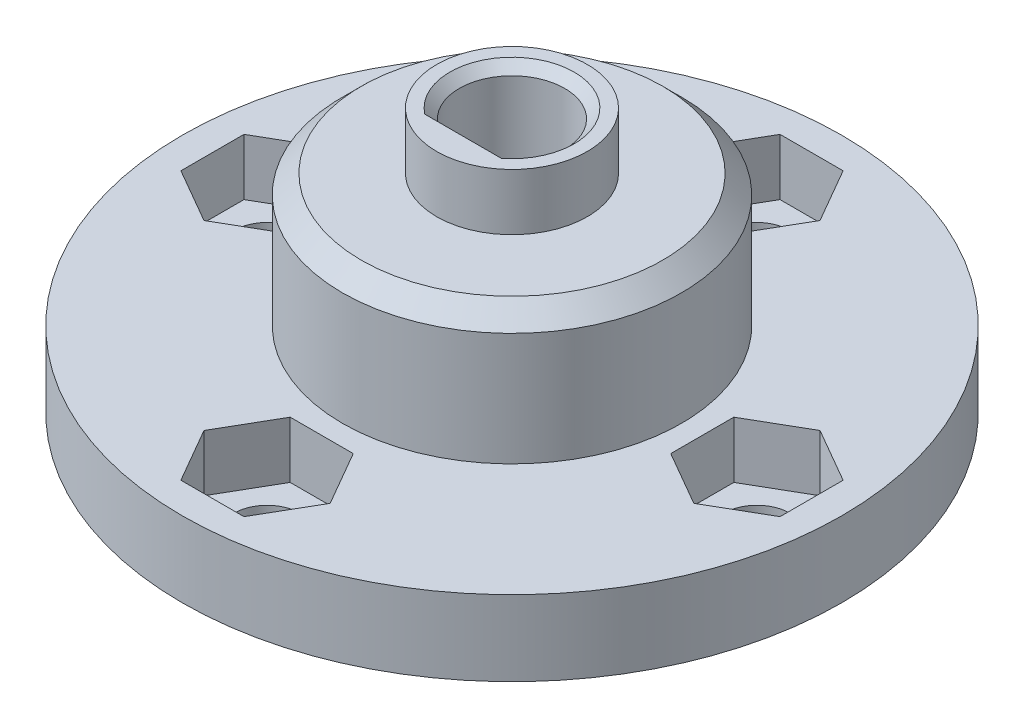
SolidWorks part; units mm, degrees
ref_plane "Спереди" through (0, 0, 0) normal (0, 0, 1) x (1, 0, 0)
ref_plane "Сверху" through (0, 0, 0) normal (0, 1, 0) x (1, 0, 0)
ref_plane "Справа" through (0, 0, 0) normal (1, 0, 0) x (0, 0, -1)
sketch "Эскиз1" plane through (0, 0, 0) normal (0, 1, 0) x (1, 0, 0)
  circle A0 centre (13, 0) radius 1.75
  circle A1 centre (0, -13) radius 1.75
  circle A2 centre (-13, 0) radius 1.75
  circle A3 centre (0, 13) radius 1.75
  circle A4 centre (0, 0) radius 17.5
  dimension "D1" = 35
extrude "Бобышка-Вытянуть1" add sketch "Эскиз1" along normal blind 4
sketch "Эскиз2" plane through (0, 4, 0) normal (0, 1, 0) x (1, 0, 0)
  line L0 (0, 17.5) -> (0, -17.5) construction
  line L1 (3.3486, 13) -> (1.6743, 15.9)
  line L2 (1.6743, 15.9) -> (-1.6743, 15.9)
  line L3 (-1.6743, 15.9) -> (-3.3486, 13)
  line L4 (-3.3486, 13) -> (-1.6743, 10.1)
  line L5 (-1.6743, 10.1) -> (1.6743, 10.1)
  line L6 (1.6743, 10.1) -> (3.3486, 13)
  line L7 (-13, -3.3486) -> (-10.1, -1.6743)
  line L8 (-10.1, -1.6743) -> (-10.1, 1.6743)
  line L9 (-10.1, 1.6743) -> (-13, 3.3486)
  line L10 (-13, 3.3486) -> (-15.9, 1.6743)
  line L11 (-15.9, 1.6743) -> (-15.9, -1.6743)
  line L12 (-15.9, -1.6743) -> (-13, -3.3486)
  line L13 (-17.5, 0) -> (17.5, 0) construction
  line L14 (15.9, -1.6743) -> (13, -3.3486)
  line L15 (15.9, 1.6743) -> (15.9, -1.6743)
  line L16 (13, 3.3486) -> (15.9, 1.6743)
  line L17 (10.1, 1.6743) -> (13, 3.3486)
  line L18 (10.1, -1.6743) -> (10.1, 1.6743)
  line L19 (13, -3.3486) -> (10.1, -1.6743)
  line L20 (1.6743, -10.1) -> (3.3486, -13)
  line L21 (-1.6743, -10.1) -> (1.6743, -10.1)
  line L22 (-3.3486, -13) -> (-1.6743, -10.1)
  line L23 (-1.6743, -15.9) -> (-3.3486, -13)
  line L24 (1.6743, -15.9) -> (-1.6743, -15.9)
  line L25 (3.3486, -13) -> (1.6743, -15.9)
  circle A0 centre (0, 13) radius 2.9 construction
  circle A1 centre (-13, 0) radius 2.9 construction
  circle A2 centre (0, 0) radius 17.5 construction
  circle A3 centre (13, 0) radius 2.9 construction
  circle A4 centre (0, -13) radius 2.9 construction
  dimension "D1" = 5.8
  dimension "D2" = 5.8
extrude "Вырез-Вытянуть1" cut sketch "Эскиз2" against normal blind 3
sketch "Эскиз3" plane through (0, 4, 0) normal (0, 1, 0) x (1, 0, 0)
  line L0 (-1.852, -2.1) -> (1.852, -2.1)
  circle A0 centre (0, 0) radius 9
  arc A1 (1.852, -2.1) -> (-1.852, -2.1) centre (0, 0) ccw
  point P4 (0, -2.1)
  point P5 (0, 2.8)
  dimension "D1" = 18
  dimension "D2" = 5.6
  dimension "D3" = 4.9
extrude "Бобышка-Вытянуть2" add sketch "Эскиз3" along normal blind 7
sketch "Эскиз4" plane through (0, 4, 0) normal (0, 1, 0) x (1, 0, 0)
  line L0 (-1.852, -2.1) -> (1.852, -2.1)
  arc A0 (1.852, -2.1) -> (-1.852, -2.1) centre (0, 0) ccw
  point P1 (0, 2.8)
extrude "Вырез-Вытянуть2" cut sketch "Эскиз4" against normal blind 2
sketch "Эскиз6" plane through (0, 11, 0) normal (0, 1, 0) x (1, 0, 0)
  line L0 (-1.852, -2.1) -> (1.852, -2.1)
  circle A0 centre (0, 0) radius 4
  arc A1 (1.852, -2.1) -> (-1.852, -2.1) centre (0, 0) ccw
  dimension "D1" = 8
extrude "Бобышка-Вытянуть3" add sketch "Эскиз6" along normal blind 3
chamfer "Фаска1" distance 1 angle 45 1 edges at (0, 11, 9)
chamfer "Фаска2" distance 0.5 angle 45 2 edges at (0, 14, 2.1) (0, 14, -2.8)
